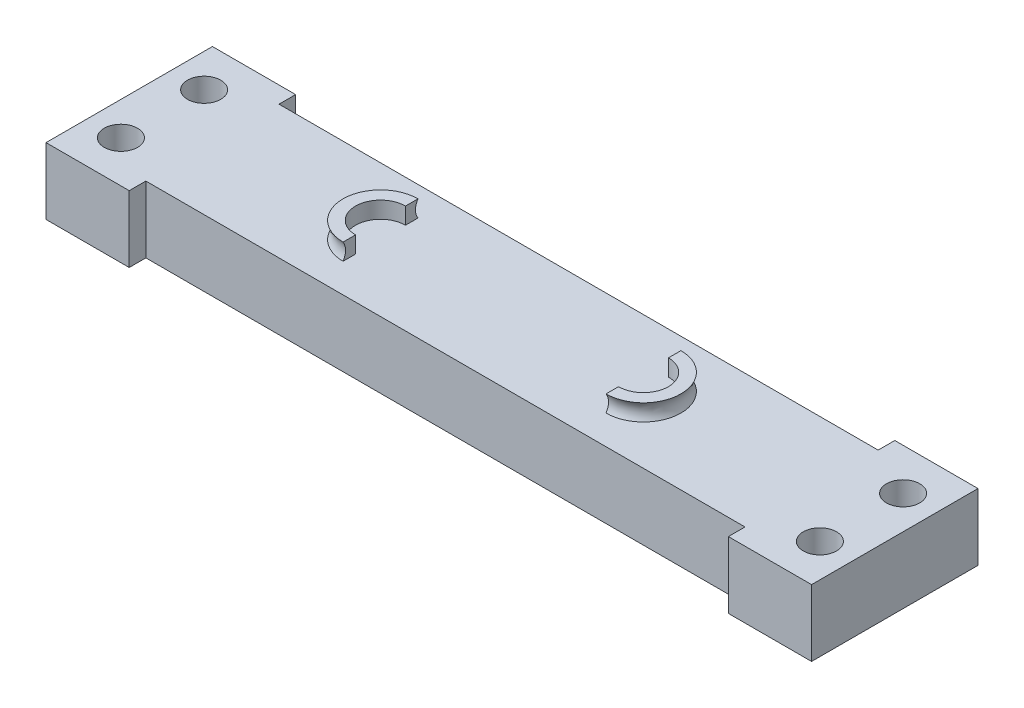
SolidWorks part; units mm, degrees
ref_plane "前视基准面" through (0, 0, 0) normal (0, 0, 1) x (1, 0, 0)
ref_plane "上视基准面" through (0, 0, 0) normal (0, 1, 0) x (1, 0, 0)
ref_plane "右视基准面" through (0, 0, 0) normal (1, 0, 0) x (0, 0, -1)
sketch "草图1" plane through (0, 0, 0) normal (0, 1, 0) x (1, 0, 0)
  line L0 (-24.9943, 0) -> (11.0057, 0)
  line L1 (11.0057, 0) -> (11.0057, 1)
  line L2 (-24.9943, 1) -> (-29.9943, 1)
  line L3 (-29.9943, 1) -> (-29.9943, -9)
  line L4 (-29.9943, -9) -> (-24.9943, -9)
  line L5 (11.0057, -9) -> (11.0057, -8)
  line L6 (11.0057, -8) -> (-24.9943, -8)
  line L7 (-24.9943, -8) -> (-24.9943, -9)
  line L8 (11.0057, -9) -> (16.0057, -9)
  line L9 (16.0057, -9) -> (16.0057, 1)
  line L10 (16.0057, 1) -> (11.0057, 1)
  line L11 (-24.9943, 1) -> (-24.9943, 0)
  circle A0 centre (-27.9943, -6.5) radius 1
  circle A1 centre (-27.9943, -1.5) radius 1
  circle A2 centre (14.0057, -1.5) radius 1
  circle A3 centre (14.0057, -6.5) radius 1
  dimension "D5" = 2
  dimension "D6" = 2
  dimension "D11" = 2
  dimension "D12" = 2
  dimension "D1" = 8
  dimension "D2" = 36
  dimension "D3" = 36
  dimension "D7" = 1
  dimension "D8" = 1
  dimension "D9" = 1
  dimension "D10" = 1
  dimension "D13" = 42
extrude "凸台-拉伸2" add sketch "草图1" along normal blind 4
sketch "草图2" plane through (0, 4, 0) normal (0, 1, 0) x (1, 0, 0)
  line L5 (-14.8943, -4) -> (0.9057, -4) construction
  line L6 (-14.8943, -1.75) -> (0.9057, -1.75)
  line L7 (-14.8943, -6.25) -> (0.9057, -6.25)
  arc A2 (-14.8943, -1.75) -> (-14.8943, -6.25) centre (-14.8943, -4) ccw
  arc A3 (0.9057, -6.25) -> (0.9057, -1.75) centre (0.9057, -4) ccw
  point P11 (-6.9943, -4)
  dimension "D5" = 2.25
extrude "凸台-拉伸3" add sketch "草图2" along normal blind 1
sketch "草图3" plane through (0, 5, 0) normal (0, 1, 0) x (1, 0, 0)
  line L1 (0.9057, -1.75) -> (-14.8943, -1.75) construction
  line L5 (-14.8943, -2.5) -> (-14.8943, -1.75)
  line L6 (-14.8943, -1.75) -> (0.9057, -1.75)
  line L7 (0.9057, -1.75) -> (0.9057, -2.5)
  line L8 (-14.8943, -5.5) -> (-14.8943, -6.25)
  line L9 (-14.8943, -6.25) -> (0.9057, -6.25)
  line L10 (0.9057, -6.25) -> (0.9057, -5.5)
  arc A0 (0.9057, -5.5) -> (0.9057, -2.5) centre (0.9057, -4) ccw
  arc A1 (-14.8943, -5.5) -> (-14.8943, -2.5) centre (-14.8943, -4) cw
  dimension "D3" = 1.5
  dimension "D4" = 1.5
extrude "切除-拉伸2" cut sketch "草图3" against normal blind 1
sketch "草图4" plane through (-14.8943, 0, 0) normal (1, 0, 0) x (0, 0, -1)
  line L0 (-6.25, 5) -> (-6.25, 4)
  spline S0 degree 2 poles (-6.25, 5) (-5.95, 4.5) (-6.25, 4) knots 0 0 0 1 1 1
sketch "草图5" plane through (0, 5, 0) normal (0, 1, 0) x (1, 0, 0)
  circle A0 centre (-14.8943, -4) radius 2.25
sweep "切除-扫描2" cut profiles "草图4" path "草图5"
sketch "草图8" plane through (0.9057, 0, 0) normal (-1, 0, 0) x (0, 0, 1)
  line L0 (6.25, 4) -> (6.25, 5)
  spline S0 degree 2 poles (6.25, 4) (5.95, 4.5) (6.25, 5) knots 0 0 0 1 1 1
sketch "草图9" plane through (0, 5, 0) normal (0, 1, 0) x (1, 0, 0)
  circle A0 centre (0.9057, -4) radius 2.25
sweep "切除-扫描3" cut profiles "草图8" path "草图9"
